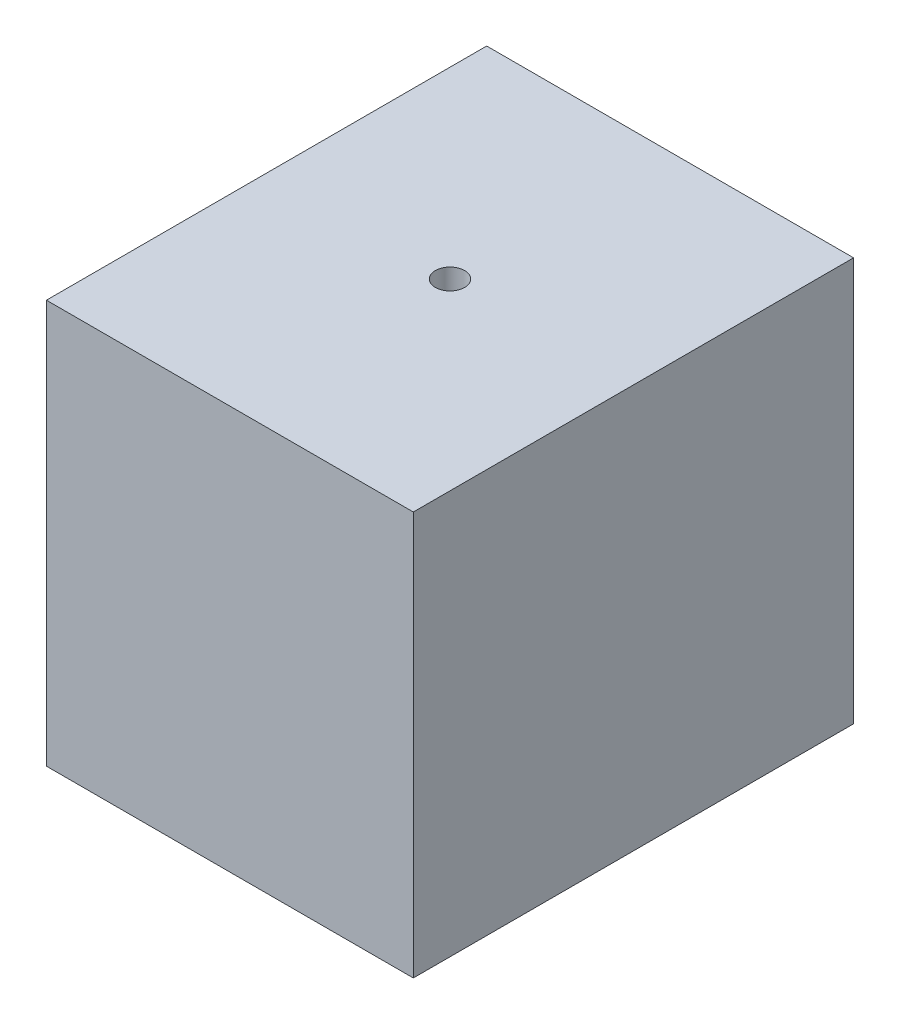
SolidWorks part; units mm, degrees
ref_plane "前视基准面" through (0, 0, 0) normal (0, 0, 1) x (1, 0, 0)
ref_plane "上视基准面" through (0, 0, 0) normal (0, 1, 0) x (1, 0, 0)
ref_plane "右视基准面" through (0, 0, 0) normal (1, 0, 0) x (0, 0, -1)
sketch "草图1" plane through (0, 0, 0) normal (0, 0, 1) x (1, 0, 0)
  line L1 (-25, 27.5) -> (25, 27.5)
  line L2 (-25, 27.5) -> (-25, -27.5)
  line L3 (-25, -27.5) -> (25, -27.5)
  line L4 (25, 27.5) -> (25, -27.5)
  line L5 (-25, 27.5) -> (25, -27.5) construction
  line L6 (-25, -27.5) -> (25, 27.5) construction
  point P0 (0, 0)
  dimension "D1" = 55
  dimension "D2" = 50
extrude "凸台-拉伸1" add sketch "草图1" along normal mid plane 60
sketch "草图2" plane through (0, 0, -30) normal (0, 0, -1) x (-1, 0, 0)
  line L0 (11.1803, 10) -> (-11.1803, 10)
  arc A0 (-11.1803, 10) -> (11.1803, 10) centre (0, 0) ccw
  dimension "D1" = 30
  dimension "D2" = 10
extrude "凸台-拉伸2" add sketch "草图2" along normal blind 10
sketch "草图3" plane through (0, 27.5, 0) normal (0, 1, 0) x (1, 0, 0)
  circle A0 centre (0, 0) radius 2
  dimension "D1" = 4
extrude "切除-拉伸1" cut sketch "草图3" against normal blind 10
